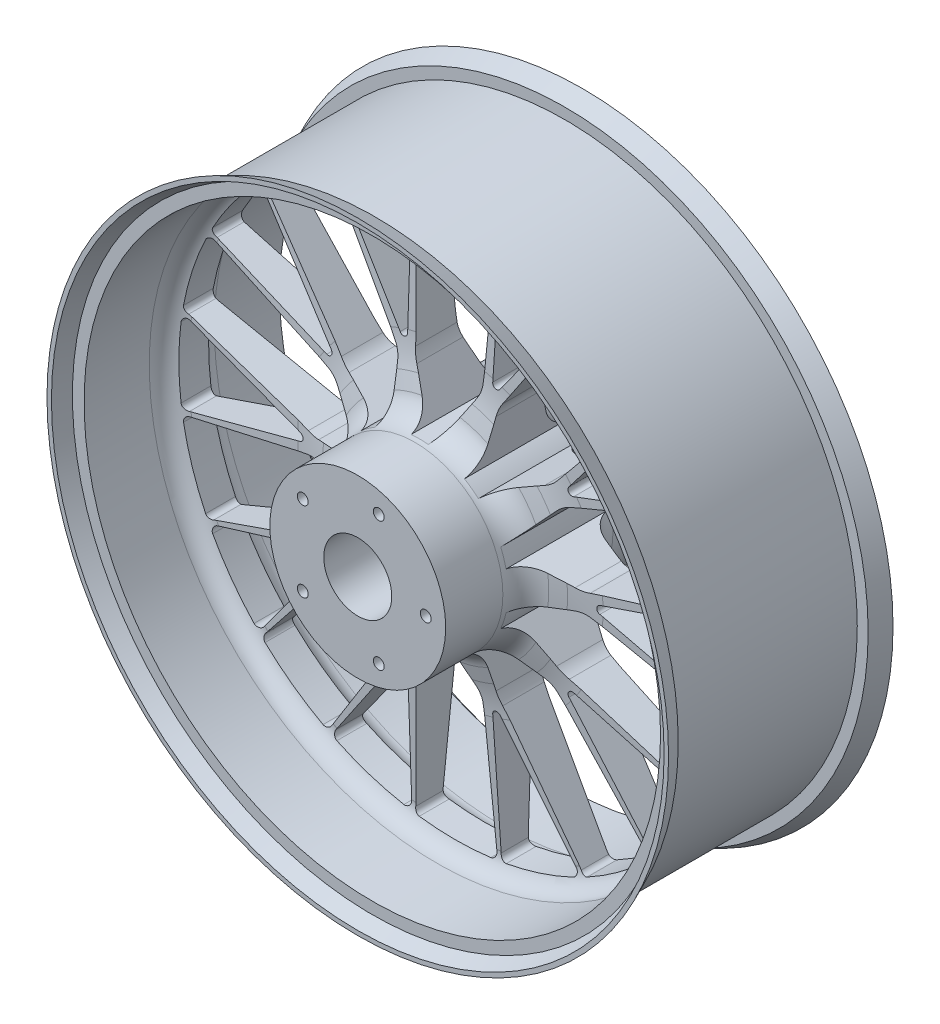
SolidWorks part; units mm, degrees
material "7050-T7651"
ref_plane "Front Plane" through (0, 0, 0) normal (0, 0, 1) x (1, 0, 0)
ref_plane "Top Plane" through (0, 0, 0) normal (0, 1, 0) x (1, 0, 0)
ref_plane "Right Plane" through (0, 0, 0) normal (1, 0, 0) x (0, 0, -1)
sketch "Sketch1" plane through (0, 0, 0) normal (0, 0, 1) x (1, 0, 0)
  line L0 (0, 0) -> (0, 203.2) construction
  line L1 (-29.8081, 197.311) -> (-24.756, 100.9121)
  line L2 (-22.1039, 91.9588) -> (-6.3592, 64.6882)
  line L3 (91.8613, 177.1487) -> (39.2866, 96.1908)
  line L4 (22.1039, 91.9588) -> (6.3592, 64.6882)
  line L5 (29.8081, 197.311) -> (24.756, 100.9121)
  line L6 (0, 0) -> (-75.5575, 232.5421) construction
  line L7 (-31.3013, 105.6196) -> (-32.8759, 195.8269)
  line L8 (-36.7583, 103.8465) -> (-88.471, 177.7703)
  line L9 (36.1696, 87.3886) -> (32.878, 56.0717)
  line L10 (71.9345, 61.4039) -> (43.1675, 48.596)
  line L11 (140.0918, 142.1072) -> (79.3427, 67.0884)
  line L12 (36.7583, 103.8465) -> (88.507, 177.7513)
  line L13 (31.3013, 105.6196) -> (32.9162, 195.8211)
  line L14 (0, 0) -> (119.438, 164.3923) construction
  line L15 (0, 0) -> (75.5575, 232.5421) construction
  line L16 (178.4427, 89.3216) -> (88.3231, 54.7279)
  line L17 (80.6276, 49.4389) -> (59.557, 26.0377)
  line L18 (94.2886, 7.3948) -> (63.4872, 13.9418)
  line L19 (196.8651, 32.6233) -> (103.6232, 7.6392)
  line L20 (90.7776, 62.4076) -> (176.0833, 91.7807)
  line L21 (87.405, 67.0496) -> (141.7305, 139.075)
  line L22 (0, 0) -> (193.2547, 62.7923) construction
  line L23 (0, 0) -> (197.8121, 143.7189) construction
  line L24 (196.8651, -32.6233) -> (103.6232, -7.6392)
  line L25 (94.2886, -7.3948) -> (63.4872, -13.9418)
  line L26 (80.6276, -49.4389) -> (59.557, -26.0377)
  line L27 (178.4427, -89.3216) -> (88.3231, -54.7279)
  line L28 (110.1229, -2.8689) -> (196.4017, -29.247)
  line L29 (110.1229, 2.8689) -> (196.4086, 29.2069)
  line L30 (0, 0) -> (193.2547, -62.7923) construction
  line L31 (0, 0) -> (244.5092, 0) construction
  line L32 (140.0918, -142.1072) -> (79.3427, -67.0884)
  line L33 (71.9345, -61.4039) -> (43.1675, -48.596)
  line L34 (36.1696, -87.3886) -> (32.878, -56.0717)
  line L35 (91.8613, -177.1487) -> (39.2866, -96.1908)
  line L36 (87.405, -67.0496) -> (141.7014, -139.1033)
  line L37 (90.7776, -62.4076) -> (176.0653, -91.8172)
  line L38 (0, 0) -> (119.438, -164.3923) construction
  line L39 (0, 0) -> (197.8121, -143.7189) construction
  line L40 (29.8081, -197.311) -> (24.756, -100.9121)
  line L41 (22.1039, -91.9588) -> (6.3592, -64.6882)
  line L42 (-22.1039, -91.9588) -> (-6.3592, -64.6882)
  line L43 (-29.8081, -197.311) -> (-24.756, -100.9121)
  line L44 (31.3013, -105.6196) -> (32.8759, -195.8269)
  line L45 (36.7583, -103.8465) -> (88.471, -177.7703)
  line L46 (0, 0) -> (0, -203.2) construction
  line L47 (0, 0) -> (75.5575, -232.5421) construction
  line L48 (-91.8613, -177.1487) -> (-39.2866, -96.1908)
  line L49 (-36.1696, -87.3886) -> (-32.878, -56.0717)
  line L50 (-71.9345, -61.4039) -> (-43.1675, -48.596)
  line L51 (-140.0918, -142.1072) -> (-79.3427, -67.0884)
  line L52 (-36.7583, -103.8465) -> (-88.507, -177.7513)
  line L53 (-31.3013, -105.6196) -> (-32.9162, -195.8211)
  line L54 (0, 0) -> (-119.438, -164.3923) construction
  line L55 (0, 0) -> (-75.5575, -232.5421) construction
  line L56 (-178.4427, -89.3216) -> (-88.3231, -54.7279)
  line L57 (-80.6276, -49.4389) -> (-59.557, -26.0377)
  line L58 (-94.2886, -7.3948) -> (-63.4872, -13.9418)
  line L59 (-196.8651, -32.6233) -> (-103.6232, -7.6392)
  line L60 (-90.7776, -62.4076) -> (-176.0833, -91.7807)
  line L61 (-87.405, -67.0496) -> (-141.7305, -139.075)
  line L62 (0, 0) -> (-193.2547, -62.7923) construction
  line L63 (0, 0) -> (-197.8121, -143.7189) construction
  line L64 (-196.8651, 32.6233) -> (-103.6232, 7.6392)
  line L65 (-94.2886, 7.3948) -> (-63.4872, 13.9418)
  line L66 (-80.6276, 49.4389) -> (-59.557, 26.0377)
  line L67 (-178.4427, 89.3216) -> (-88.3231, 54.7279)
  line L68 (-110.1229, 2.8689) -> (-196.4017, 29.247)
  line L69 (-110.1229, -2.8689) -> (-196.4086, -29.2069)
  line L70 (0, 0) -> (-193.2547, 62.7923) construction
  line L71 (0, 0) -> (-244.5092, 0) construction
  line L72 (-140.0918, 142.1072) -> (-79.3427, 67.0884)
  line L73 (-71.9345, 61.4039) -> (-43.1675, 48.596)
  line L74 (-36.1696, 87.3886) -> (-32.878, 56.0717)
  line L75 (-91.8613, 177.1487) -> (-39.2866, 96.1908)
  line L76 (-87.405, 67.0496) -> (-141.7014, 139.1033)
  line L77 (-90.7776, 62.4076) -> (-176.0653, 91.8172)
  line L78 (0, 0) -> (-119.438, 164.3923) construction
  line L79 (0, 0) -> (-197.8121, 143.7189) construction
  circle A0 centre (0, 0) radius 25
  arc A1 (26.3319, 201.4867) -> (-26.3319, 201.4867) centre (0, 0) ccw
  arc A2 (6.3592, 64.6882) -> (-6.3592, 64.6882) centre (0, 0) ccw
  arc A3 (-31.3013, 105.6196) -> (-33.3738, 102.7141) centre (-34.3009, 105.5673) cw
  arc A4 (-36.7583, 103.8465) -> (-33.3738, 102.7141) centre (-34.3009, 105.5673) ccw
  arc A5 (22.1039, 91.9588) -> (24.756, 100.9121) centre (4.7834, 101.9588) ccw
  arc A6 (-24.756, 100.9121) -> (-22.1039, 91.9588) centre (-4.7834, 101.9588) ccw
  arc A7 (-37.6158, 199.688) -> (-86.9041, 183.6788) centre (0, 0) ccw
  arc A8 (29.8081, 197.311) -> (26.3319, 201.4867) centre (25.8136, 197.5204) ccw
  arc A9 (-29.8081, 197.311) -> (-26.3319, 201.4867) centre (-25.8136, 197.5204) cw
  arc A10 (-32.8759, 195.8269) -> (-37.6158, 199.688) centre (-36.8753, 195.7571) ccw
  arc A11 (-88.471, 177.7703) -> (-86.9041, 183.6788) centre (-85.1934, 180.0631) cw
  arc A12 (139.7338, 147.5286) -> (97.1279, 178.4836) centre (0, 0) ccw
  arc A13 (43.1675, 48.596) -> (32.878, 56.0717) centre (0, 0) ccw
  arc A14 (36.7583, 103.8465) -> (33.3738, 102.7141) centre (34.3009, 105.5673) cw
  arc A15 (31.3013, 105.6196) -> (33.3738, 102.7141) centre (34.3009, 105.5673) ccw
  arc A16 (71.9345, 61.4039) -> (79.3427, 67.0884) centre (63.7998, 79.6748) ccw
  arc A17 (39.2866, 96.1908) -> (36.1696, 87.3886) centre (56.06, 85.2981) ccw
  arc A18 (86.9419, 183.661) -> (37.6568, 199.6803) centre (0, 0) ccw
  arc A19 (140.0918, 142.1072) -> (139.7338, 147.5286) centre (136.9832, 144.6245) ccw
  arc A20 (91.8613, 177.1487) -> (97.1279, 178.4836) centre (95.216, 174.9702) cw
  arc A21 (88.507, 177.7513) -> (86.9419, 183.661) centre (85.2304, 180.0456) ccw
  arc A22 (32.9162, 195.8211) -> (37.6568, 199.6803) centre (36.9156, 195.7495) cw
  arc A23 (199.7622, 37.2197) -> (183.4882, 87.3059) centre (0, 0) ccw
  arc A24 (63.4872, 13.9418) -> (59.557, 26.0377) centre (0, 0) ccw
  arc A25 (90.7776, 62.4076) -> (87.3738, 63.4808) centre (89.8009, 65.2442) cw
  arc A26 (87.405, 67.0496) -> (87.3738, 63.4808) centre (89.8009, 65.2442) ccw
  arc A27 (94.2886, 7.3948) -> (103.6232, 7.6392) centre (98.4468, 26.9577) ccw
  arc A28 (88.3231, 54.7279) -> (80.6276, 49.4389) centre (95.4905, 36.0563) ccw
  arc A29 (178.2906, 97.4817) -> (147.8341, 139.4106) centre (0, 0) ccw
  arc A30 (196.8651, 32.6233) -> (199.7622, 37.2197) centre (195.8299, 36.487) ccw
  arc A31 (178.4427, 89.3216) -> (183.4882, 87.3059) centre (179.8762, 85.5873) cw
  arc A32 (176.0833, 91.7807) -> (178.2906, 97.4817) centre (174.781, 95.5628) ccw
  arc A33 (141.7305, 139.075) -> (147.8341, 139.4106) centre (144.924, 136.6663) cw
  arc A34 (183.4882, -87.3059) -> (199.7622, -37.2197) centre (0, 0) ccw
  arc A35 (59.557, -26.0377) -> (63.4872, -13.9418) centre (0, 0) ccw
  arc A36 (110.1229, -2.8689) -> (108, 0) centre (111, 0) cw
  arc A37 (110.1229, 2.8689) -> (108, 0) centre (111, 0) ccw
  arc A38 (80.6276, -49.4389) -> (88.3231, -54.7279) centre (95.4905, -36.0563) ccw
  arc A39 (103.6232, -7.6392) -> (94.2886, -7.3948) centre (98.4468, -26.9577) ccw
  arc A40 (201.5385, -25.9323) -> (201.5438, 25.8908) centre (0, 0) ccw
  arc A41 (178.4427, -89.3216) -> (183.4882, -87.3059) centre (179.8762, -85.5873) ccw
  arc A42 (196.8651, -32.6233) -> (199.7622, -37.2197) centre (195.8299, -36.487) cw
  arc A43 (196.4017, -29.247) -> (201.5385, -25.9323) centre (197.5712, -25.4218) ccw
  arc A44 (196.4086, 29.2069) -> (201.5438, 25.8908) centre (197.5764, 25.3812) cw
  arc A45 (97.1279, -178.4836) -> (139.7338, -147.5286) centre (0, 0) ccw
  arc A46 (32.878, -56.0717) -> (43.1675, -48.596) centre (0, 0) ccw
  arc A47 (87.405, -67.0496) -> (87.3738, -63.4808) centre (89.8009, -65.2442) cw
  arc A48 (90.7776, -62.4076) -> (87.3738, -63.4808) centre (89.8009, -65.2442) ccw
  arc A49 (36.1696, -87.3886) -> (39.2866, -96.1908) centre (56.06, -85.2981) ccw
  arc A50 (79.3427, -67.0884) -> (71.9345, -61.4039) centre (63.7998, -79.6748) ccw
  arc A51 (147.8055, -139.441) -> (178.2706, -97.5184) centre (0, 0) ccw
  arc A52 (91.8613, -177.1487) -> (97.1279, -178.4836) centre (95.216, -174.9702) ccw
  arc A53 (140.0918, -142.1072) -> (139.7338, -147.5286) centre (136.9832, -144.6245) cw
  arc A54 (141.7014, -139.1033) -> (147.8055, -139.441) centre (144.8959, -136.6961) ccw
  arc A55 (176.0653, -91.8172) -> (178.2706, -97.5184) centre (174.7613, -95.5987) cw
  arc A56 (-26.3319, -201.4867) -> (26.3319, -201.4867) centre (0, 0) ccw
  arc A57 (-6.3592, -64.6882) -> (6.3592, -64.6882) centre (0, 0) ccw
  arc A58 (31.3013, -105.6196) -> (33.3738, -102.7141) centre (34.3009, -105.5673) cw
  arc A59 (36.7583, -103.8465) -> (33.3738, -102.7141) centre (34.3009, -105.5673) ccw
  arc A60 (-22.1039, -91.9588) -> (-24.756, -100.9121) centre (-4.7834, -101.9588) ccw
  arc A61 (24.756, -100.9121) -> (22.1039, -91.9588) centre (4.7834, -101.9588) ccw
  arc A62 (37.6158, -199.688) -> (86.9041, -183.6788) centre (0, 0) ccw
  arc A63 (-29.8081, -197.311) -> (-26.3319, -201.4867) centre (-25.8136, -197.5204) ccw
  arc A64 (29.8081, -197.311) -> (26.3319, -201.4867) centre (25.8136, -197.5204) cw
  arc A65 (32.8759, -195.8269) -> (37.6158, -199.688) centre (36.8753, -195.7571) ccw
  arc A66 (88.471, -177.7703) -> (86.9041, -183.6788) centre (85.1934, -180.0631) cw
  arc A67 (-139.7338, -147.5286) -> (-97.1279, -178.4836) centre (0, 0) ccw
  arc A68 (-43.1675, -48.596) -> (-32.878, -56.0717) centre (0, 0) ccw
  arc A69 (-36.7583, -103.8465) -> (-33.3738, -102.7141) centre (-34.3009, -105.5673) cw
  arc A70 (-31.3013, -105.6196) -> (-33.3738, -102.7141) centre (-34.3009, -105.5673) ccw
  arc A71 (-71.9345, -61.4039) -> (-79.3427, -67.0884) centre (-63.7998, -79.6748) ccw
  arc A72 (-39.2866, -96.1908) -> (-36.1696, -87.3886) centre (-56.06, -85.2981) ccw
  arc A73 (-86.9419, -183.661) -> (-37.6568, -199.6803) centre (0, 0) ccw
  arc A74 (-140.0918, -142.1072) -> (-139.7338, -147.5286) centre (-136.9832, -144.6245) ccw
  arc A75 (-91.8613, -177.1487) -> (-97.1279, -178.4836) centre (-95.216, -174.9702) cw
  arc A76 (-88.507, -177.7513) -> (-86.9419, -183.661) centre (-85.2304, -180.0456) ccw
  arc A77 (-32.9162, -195.8211) -> (-37.6568, -199.6803) centre (-36.9156, -195.7495) cw
  arc A78 (-199.7622, -37.2197) -> (-183.4882, -87.3059) centre (0, 0) ccw
  arc A79 (-63.4872, -13.9418) -> (-59.557, -26.0377) centre (0, 0) ccw
  arc A80 (-90.7776, -62.4076) -> (-87.3738, -63.4808) centre (-89.8009, -65.2442) cw
  arc A81 (-87.405, -67.0496) -> (-87.3738, -63.4808) centre (-89.8009, -65.2442) ccw
  arc A82 (-94.2886, -7.3948) -> (-103.6232, -7.6392) centre (-98.4468, -26.9577) ccw
  arc A83 (-88.3231, -54.7279) -> (-80.6276, -49.4389) centre (-95.4905, -36.0563) ccw
  arc A84 (-178.2906, -97.4817) -> (-147.8341, -139.4106) centre (0, 0) ccw
  arc A85 (-196.8651, -32.6233) -> (-199.7622, -37.2197) centre (-195.8299, -36.487) ccw
  arc A86 (-178.4427, -89.3216) -> (-183.4882, -87.3059) centre (-179.8762, -85.5873) cw
  arc A87 (-176.0833, -91.7807) -> (-178.2906, -97.4817) centre (-174.781, -95.5628) ccw
  arc A88 (-141.7305, -139.075) -> (-147.8341, -139.4106) centre (-144.924, -136.6663) cw
  arc A89 (-183.4882, 87.3059) -> (-199.7622, 37.2197) centre (0, 0) ccw
  arc A90 (-59.557, 26.0377) -> (-63.4872, 13.9418) centre (0, 0) ccw
  arc A91 (-110.1229, 2.8689) -> (-108, 0) centre (-111, 0) cw
  arc A92 (-110.1229, -2.8689) -> (-108, 0) centre (-111, 0) ccw
  arc A93 (-80.6276, 49.4389) -> (-88.3231, 54.7279) centre (-95.4905, 36.0563) ccw
  arc A94 (-103.6232, 7.6392) -> (-94.2886, 7.3948) centre (-98.4468, 26.9577) ccw
  arc A95 (-201.5385, 25.9323) -> (-201.5438, -25.8908) centre (0, 0) ccw
  arc A96 (-178.4427, 89.3216) -> (-183.4882, 87.3059) centre (-179.8762, 85.5873) ccw
  arc A97 (-196.8651, 32.6233) -> (-199.7622, 37.2197) centre (-195.8299, 36.487) cw
  arc A98 (-196.4017, 29.247) -> (-201.5385, 25.9323) centre (-197.5712, 25.4218) ccw
  arc A99 (-196.4086, -29.2069) -> (-201.5438, -25.8908) centre (-197.5764, -25.3812) cw
  arc A100 (-97.1279, 178.4836) -> (-139.7338, 147.5286) centre (0, 0) ccw
  arc A101 (-32.878, 56.0717) -> (-43.1675, 48.596) centre (0, 0) ccw
  arc A102 (-87.405, 67.0496) -> (-87.3738, 63.4808) centre (-89.8009, 65.2442) cw
  arc A103 (-90.7776, 62.4076) -> (-87.3738, 63.4808) centre (-89.8009, 65.2442) ccw
  arc A104 (-36.1696, 87.3886) -> (-39.2866, 96.1908) centre (-56.06, 85.2981) ccw
  arc A105 (-79.3427, 67.0884) -> (-71.9345, 61.4039) centre (-63.7998, 79.6748) ccw
  arc A106 (-147.8055, 139.441) -> (-178.2706, 97.5184) centre (0, 0) ccw
  arc A107 (-91.8613, 177.1487) -> (-97.1279, 178.4836) centre (-95.216, 174.9702) ccw
  arc A108 (-140.0918, 142.1072) -> (-139.7338, 147.5286) centre (-136.9832, 144.6245) cw
  arc A109 (-141.7014, 139.1033) -> (-147.8055, 139.441) centre (-144.8959, 136.6961) ccw
  arc A110 (-176.0653, 91.8172) -> (-178.2706, 97.5184) centre (-174.7613, 95.5987) cw
  circle A111 centre (0, 0) radius 228.6
  circle A112 centre (0, 0) radius 50 construction
  circle A113 centre (15.4508, 47.5528) radius 4
  circle A114 centre (50, 0) radius 4
  circle A115 centre (15.4508, -47.5528) radius 4
  circle A116 centre (-40.4508, -29.3893) radius 4
  circle A117 centre (-40.4508, 29.3893) radius 4
  point P11 (0, 53.8255)
  point P23 (24.5047, 96.1171)
  point P26 (-24.5047, 96.1171)
  point P27 (30, 200.9732)
  point P30 (-30, 200.9732)
  point P33 (-33, 200.5025)
  point P36 (-91.1548, 181.6068)
  point P48 (31.6378, 43.5457)
  point P77 (51.1911, 16.633)
  point P106 (51.1911, -16.633)
  point P135 (31.6378, -43.5457)
  point P164 (0, -53.8255)
  point P193 (-31.6378, -43.5457)
  point P222 (-51.1911, -16.633)
  point P251 (-51.1911, 16.633)
  point P280 (-31.6378, 43.5457)
  dimension "D1" = 50
  dimension "D2" = 406.4
  dimension "D3" = 130
  dimension "D11" = 3
  dimension "D12" = 20
  dimension "D13" = 4
  dimension "D15" = 457.2
  dimension "D16" = 100
  dimension "D17" = 8
  dimension "D19" = 108
  dimension "D4" = 6
  dimension "D5" = 105
  dimension "D6" = 60
  dimension "D7" = 3
  dimension "D8" = 18
  dimension "D9" = 30
  dimension "D10" = 2
  dimension "D14" = 10
  dimension "D18" = 5
extrude "Boss-Extrude1" add sketch "Sketch1" along normal mid plane 165.1
sketch "Sketch2" plane through (0, 0, 0) normal (1, 0, 0) x (0, 0, -1)
  line L0 (0, 0) -> (0, 217.623) construction
  line L1 (-10, 197.311) -> (-14.4558, 112.2901)
  line L2 (-82.55, 100.9121) -> (82.55, 100.9121) construction
  line L3 (-82.55, 228.6) -> (82.55, 228.6)
  line L4 (-82.55, 197.311) -> (82.55, 197.311) construction
  line L5 (-71.85, 212) -> (-23.9393, 212)
  line L6 (-82.55, 228.6) -> (-82.55, -228.6) construction
  line L8 (-18.1925, 89.9599) -> (-21.2849, 79.1754)
  line L9 (-82.55, 64.6882) -> (82.55, 64.6882) construction
  line L10 (-40.5102, 64.6882) -> (-82.55, 64.6882)
  line L11 (-82.55, 64.6882) -> (-82.55, 225.3213)
  line L12 (71.85, 220.6032) -> (71.85, 212)
  line L13 (40.5102, 64.6882) -> (82.55, 64.6882)
  line L14 (18.1925, 89.9599) -> (21.2849, 79.1754)
  line L15 (82.55, 225.3213) -> (71.85, 220.6032)
  line L16 (10, 197.311) -> (14.4558, 112.2901)
  line L17 (0, 0) -> (30.7585, 0) construction
  line L18 (-69.85, 215) -> (69.85, 215)
  line L20 (-69.85, 215) -> (-69.85, 223)
  line L21 (-69.85, 223) -> (-82.55, 228.6)
  line L22 (-82.55, 225.3213) -> (-71.85, 220.6032)
  line L23 (-71.85, 220.6032) -> (-71.85, 212)
  line L24 (69.85, 223) -> (82.55, 228.6)
  line L25 (69.85, 215) -> (69.85, 223)
  line L26 (82.55, 64.6882) -> (82.55, 225.3213)
  line L27 (71.85, 212) -> (23.9393, 212)
  arc A0 (-23.9393, 212) -> (-10, 197.311) centre (-23.9393, 198.0416) cw
  arc A1 (23.9393, 212) -> (10, 197.311) centre (23.9393, 198.0416) ccw
  arc A2 (40.5102, 64.6882) -> (21.2849, 79.1754) centre (40.5102, 84.6882) cw
  arc A3 (-21.2849, 79.1754) -> (-40.5102, 64.6882) centre (-40.5102, 84.6882) cw
  arc A4 (18.1925, 89.9599) -> (14.4558, 112.2901) centre (114.3187, 117.5237) cw
  arc A5 (-14.4558, 112.2901) -> (-18.1925, 89.9599) centre (-114.3187, 117.5237) cw
  point P5 (0, 228.6)
  point P31 (25.4391, 64.6882)
  point P34 (-25.4391, 64.6882)
  point P37 (15.0521, 100.9121)
  point P40 (-15.0521, 100.9121)
  point P45 (0, 215)
  dimension "D5" = 20
  dimension "D6" = 100
  dimension "D1" = 3
  dimension "D2" = 20
  dimension "D3" = 212
  dimension "D4" = 16
  dimension "D7" = 139.7
  dimension "D8" = 3
  dimension "D9" = 228.6
  dimension "D10" = 3
  dimension "D11" = 2
  dimension "D13" = 8
revolve "Cut-Revolve1" cut sketch "Sketch2" angle 360 about L17
